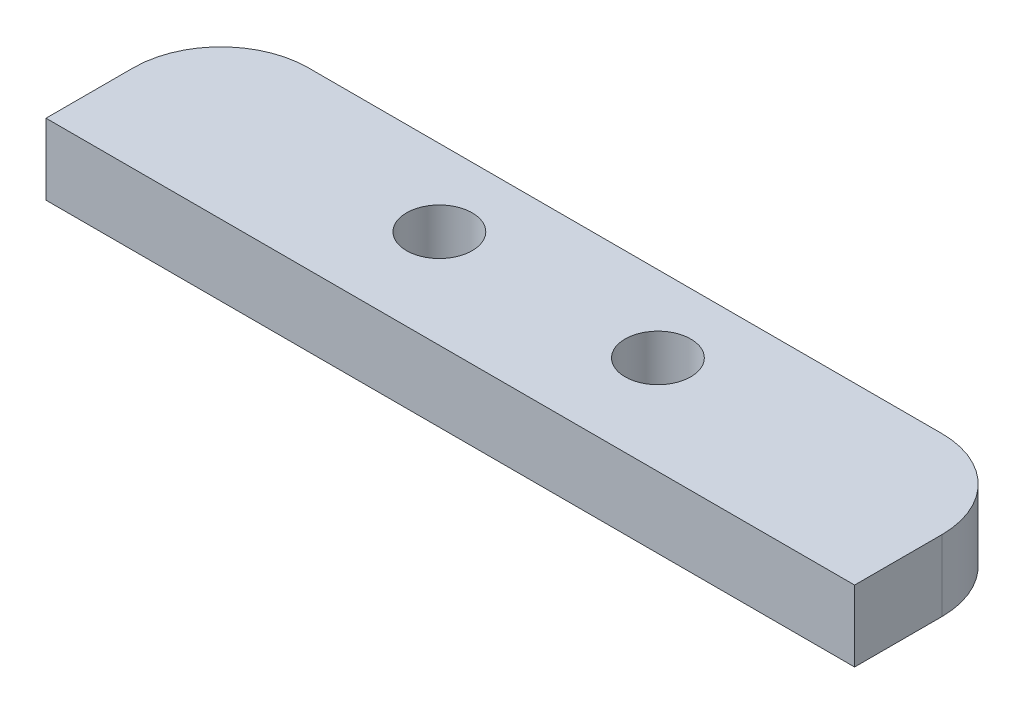
SolidWorks part; units mm, degrees
ref_plane "Front Plane" through (0, 0, 0) normal (0, 0, 1) x (1, 0, 0)
ref_plane "Top Plane" through (0, 0, 0) normal (0, 1, 0) x (1, 0, 0)
ref_plane "Right Plane" through (0, 0, 0) normal (1, 0, 0) x (0, 0, -1)
sketch "Sketch1" plane through (0, 0, 0) normal (0, 1, 0) x (1, 0, 0)
  line L0 (-18.5, 4) -> (18.5, -4) construction
  line L1 (-14.5, 4) -> (14.5, 4)
  line L2 (-18.5, 0) -> (-18.5, -4)
  line L3 (-18.5, -4) -> (18.5, -4)
  line L4 (18.5, 0) -> (18.5, -4)
  arc A1 (14.5, 4) -> (18.5, 0) centre (14.5, 0) cw
  arc A2 (-14.5, 4) -> (-18.5, 0) centre (-14.5, 0) ccw
  circle A4 centre (-5, 0.5) radius 1.5025
  circle A6 centre (5, 0.5) radius 1.5025
  point P9 (18.5, 4)
  dimension "D5" = 4
  dimension "D1" = 37
  dimension "D2" = 8
extrude "Boss-Extrude1" add sketch "Sketch1" along normal blind 3.25
